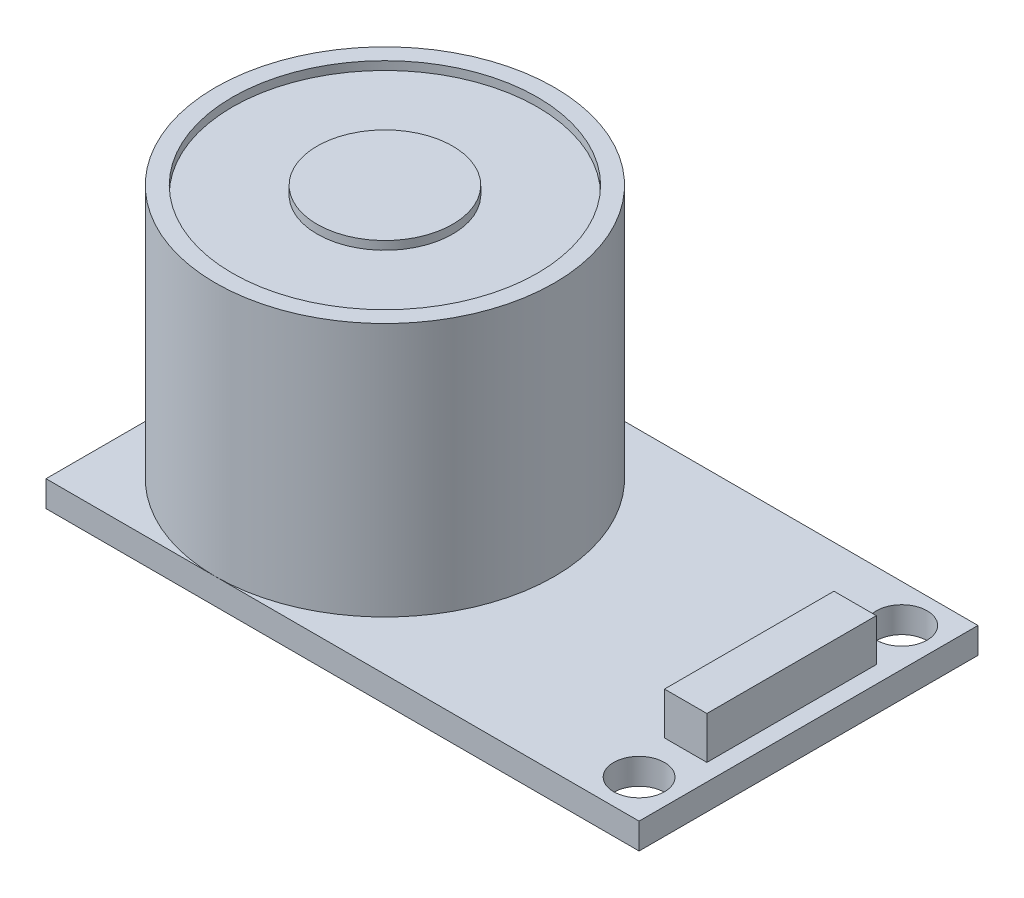
SolidWorks part; units mm, degrees
ref_plane "Front Plane" through (0, 0, 0) normal (0, 0, 1) x (1, 0, 0)
ref_plane "Top Plane" through (0, 0, 0) normal (0, 1, 0) x (1, 0, 0)
ref_plane "Right Plane" through (0, 0, 0) normal (1, 0, 0) x (0, 0, -1)
sketch "Sketch1" plane through (0, 0, 0) normal (0, 1, 0) x (1, 0, 0)
  line L0 (30.5, 20) -> (30.5, 0) construction
  line L1 (0, 0) -> (35, 0)
  line L2 (0, 0) -> (0, 20)
  line L3 (0, 20) -> (35, 20)
  line L4 (35, 0) -> (35, 20)
  line L5 (30.5, 10) -> (35, 10) construction
  circle A0 centre (32.75, 17.75) radius 1.5
  circle A1 centre (32.75, 2.25) radius 1.5
  dimension "D5" = 2.25
  dimension "D4" = 3
  dimension "D1" = 20
  dimension "D2" = 35
  dimension "D3" = 4.5
  dimension "D6" = 2.25
extrude "Boss-Extrude1" add sketch "Sketch1" along normal blind 1.53
sketch "Sketch2" plane through (0, 1.53, 0) normal (0, 1, 0) x (1, 0, 0)
  line L0 (0, 20) -> (0, 0) construction
  circle A0 centre (10, 10) radius 10
  dimension "D1" = 10
  dimension "D2" = 20
extrude "Boss-Extrude2" add sketch "Sketch2" along normal blind 15
sketch "Sketch3" plane through (0, 16.53, 0) normal (0, 1, 0) x (1, 0, 0)
  circle A0 centre (10, 10) radius 4
  circle A1 centre (10, 10) radius 9
  dimension "D1" = 8
  dimension "D2" = 18
extrude "Cut-Extrude1" cut sketch "Sketch3" against normal blind 0.5
sketch "Sketch4" plane through (0, 1.53, 0) normal (0, 1, 0) x (1, 0, 0)
  line L0 (32.75, 16.25) -> (32.75, 3.75) construction
  line L2 (31.5, 5) -> (34, 5)
  line L3 (31.5, 5) -> (31.5, 15)
  line L4 (31.5, 15) -> (34, 15)
  line L5 (34, 5) -> (34, 15)
  line L6 (31.5, 5) -> (34, 15) construction
  line L7 (31.5, 15) -> (34, 5) construction
  circle A0 centre (32.75, 17.75) radius 1.5 construction
  circle A1 centre (32.75, 2.25) radius 1.5 construction
  point P8 (32.75, 10)
  dimension "D1" = 10
  dimension "D2" = 2.5
extrude "Boss-Extrude3" add sketch "Sketch4" along normal blind 2.5
